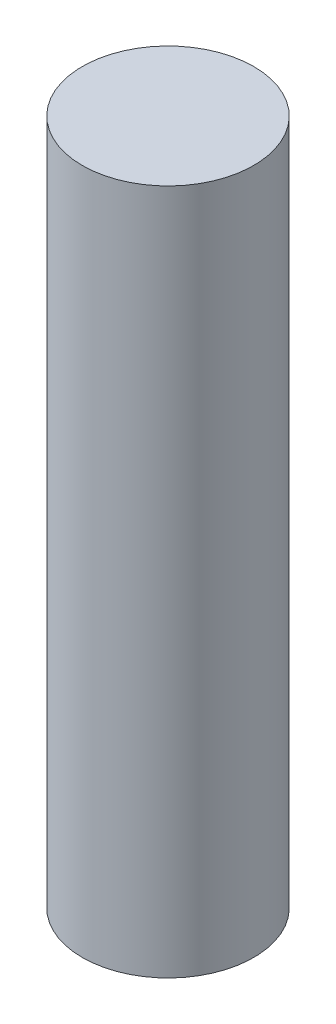
SolidWorks part; units mm, degrees
ref_plane "Plano frontal" through (0, 0, 0) normal (0, 0, 1) x (1, 0, 0)
ref_plane "Plano superior" through (0, 0, 0) normal (0, 1, 0) x (1, 0, 0)
ref_plane "Plano direito" through (0, 0, 0) normal (1, 0, 0) x (0, 0, -1)
sketch "Esboço1" plane through (0, 0, 0) normal (0, 1, 0) x (1, 0, 0)
  circle A0 centre (0, 0) radius 10
  dimension "D1" = 20
extrude "Ressalto-extrusão1" add sketch "Esboço1" along normal blind 80
cosmetic thread "Representação de rosca1" [suppressed]
